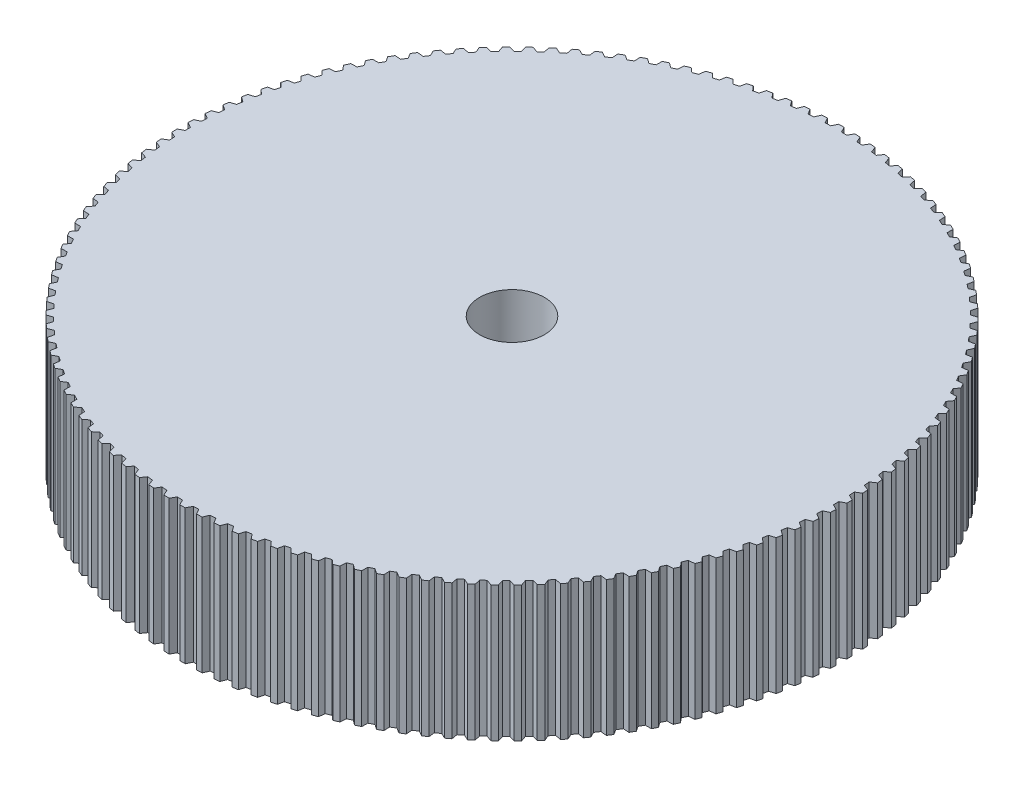
SolidWorks part; units mm, degrees
ref_plane "Front Plane" through (0, 0, 0) normal (0, 0, 1) x (1, 0, 0)
ref_plane "Top Plane" through (0, 0, 0) normal (0, 1, 0) x (1, 0, 0)
ref_plane "Right Plane" through (0, 0, 0) normal (1, 0, 0) x (0, 0, -1)
sketch "Sketch3" plane through (0, 0, 0) normal (0, 1, 0) x (1, 0, 0)
  line L0 (-0.25, 30.5) -> (0.25, 30.5)
  line L1 (0.25, 30.5) -> (0.5, 30)
  line L2 (0.5, 30) -> (-0.5, 30)
  line L3 (1.9948, 29.9378) -> (0.996, 29.9876)
  line L4 (0, 30) -> (0.5, 30)
  line L5 (1.2706, 30.4745) -> (0.996, 29.9876)
  line L6 (1.2706, 30.4745) -> (1.77, 30.4496)
  line L7 (-0.25, 30.5) -> (-0.5, 30)
  line L8 (1.77, 30.4496) -> (1.9948, 29.9378)
  line L9 (3.4846, 29.8011) -> (2.4895, 29.9007)
  line L10 (2.7881, 30.3733) -> (2.4895, 29.9007)
  line L11 (2.7881, 30.3733) -> (3.2856, 30.3235)
  line L12 (3.2856, 30.3235) -> (3.4846, 29.8011)
  line L13 (4.9657, 29.5904) -> (3.9769, 29.7394)
  line L14 (4.2986, 30.1966) -> (3.9769, 29.7394)
  line L15 (4.2986, 30.1966) -> (4.793, 30.1221)
  line L16 (4.793, 30.1221) -> (4.9657, 29.5904)
  line L17 (6.4345, 29.3061) -> (5.4543, 29.5042)
  line L18 (5.7984, 29.9448) -> (5.4543, 29.5042)
  line L19 (5.7984, 29.9448) -> (6.2885, 29.8457)
  line L20 (6.2885, 29.8457) -> (6.4345, 29.3061)
  line L21 (7.8873, 28.9489) -> (6.9182, 29.1957)
  line L22 (7.2838, 29.6185) -> (6.9182, 29.1957)
  line L23 (7.2838, 29.6185) -> (7.7684, 29.4952)
  line L24 (7.7684, 29.4952) -> (7.8873, 28.9489)
  line L25 (9.3204, 28.5198) -> (8.3649, 28.8146)
  line L26 (8.7511, 29.2187) -> (8.3649, 28.8146)
  line L27 (8.7511, 29.2187) -> (9.2289, 29.0713)
  line L28 (9.2289, 29.0713) -> (9.3204, 28.5198)
  line L29 (10.7305, 28.0198) -> (9.7908, 28.3618)
  line L30 (10.1967, 28.7461) -> (9.7908, 28.3618)
  line L31 (10.1967, 28.7461) -> (10.6665, 28.5751)
  line L32 (10.6665, 28.5751) -> (10.7305, 28.0198)
  line L33 (12.1138, 27.4501) -> (11.1923, 27.8385)
  line L34 (11.6169, 28.2021) -> (11.1923, 27.8385)
  line L35 (11.6169, 28.2021) -> (12.0776, 28.0079)
  line L36 (12.0776, 28.0079) -> (12.1138, 27.4501)
  line L37 (13.467, 26.8121) -> (12.566, 27.246)
  line L38 (13.0082, 27.588) -> (12.566, 27.246)
  line L39 (13.0082, 27.588) -> (13.4587, 27.3711)
  line L40 (13.4587, 27.3711) -> (13.467, 26.8121)
  line L41 (14.7867, 26.1075) -> (13.9085, 26.5858)
  line L42 (14.3672, 26.9053) -> (13.9085, 26.5858)
  line L43 (14.3672, 26.9053) -> (14.8063, 26.6662)
  line L44 (14.8063, 26.6662) -> (14.7867, 26.1075)
  line L45 (16.0697, 25.338) -> (15.2164, 25.8594)
  line L46 (15.6905, 26.1557) -> (15.2164, 25.8594)
  line L47 (15.6905, 26.1557) -> (16.1171, 25.895)
  line L48 (16.1171, 25.895) -> (16.0697, 25.338)
  line L49 (17.3127, 24.5055) -> (16.4865, 25.0688)
  line L50 (16.9747, 25.3411) -> (16.4865, 25.0688)
  line L51 (16.9747, 25.3411) -> (17.3878, 25.0595)
  line L52 (17.3878, 25.0595) -> (17.3127, 24.5055)
  line L53 (18.5127, 23.6121) -> (17.7156, 24.2159)
  line L54 (18.2168, 24.4635) -> (17.7156, 24.2159)
  line L55 (18.2168, 24.4635) -> (18.6153, 24.1616)
  line L56 (18.6153, 24.1616) -> (18.5127, 23.6121)
  line L57 (19.6667, 22.6599) -> (18.9006, 23.3027)
  line L58 (19.4135, 23.5251) -> (18.9006, 23.3027)
  line L59 (19.4135, 23.5251) -> (19.7965, 23.2037)
  line L60 (19.7965, 23.2037) -> (19.6667, 22.6599)
  line L61 (20.7717, 21.6515) -> (20.0387, 22.3316)
  line L62 (20.562, 22.5281) -> (20.0387, 22.3316)
  line L63 (20.562, 22.5281) -> (20.9285, 22.188)
  line L64 (20.9285, 22.188) -> (20.7717, 21.6515)
  line L65 (21.8251, 20.5892) -> (21.1269, 21.305)
  line L66 (21.6594, 21.4752) -> (21.1269, 21.305)
  line L67 (21.6594, 21.4752) -> (22.0085, 21.1173)
  line L68 (22.0085, 21.1173) -> (21.8251, 20.5892)
  line L69 (22.8243, 19.4757) -> (22.1626, 20.2255)
  line L70 (22.7029, 20.3689) -> (22.1626, 20.2255)
  line L71 (22.7029, 20.3689) -> (23.0337, 19.994)
  line L72 (23.0337, 19.994) -> (22.8243, 19.4757)
  line L73 (23.7667, 18.3138) -> (23.1432, 19.0956)
  line L74 (23.69, 19.2119) -> (23.1432, 19.0956)
  line L75 (23.69, 19.2119) -> (24.0017, 18.821)
  line L76 (24.0017, 18.821) -> (23.7667, 18.3138)
  line L77 (24.65, 17.1063) -> (24.0663, 17.9183)
  line L78 (24.6182, 18.0072) -> (24.0663, 17.9183)
  line L79 (24.6182, 18.0072) -> (24.91, 17.6012)
  line L80 (24.91, 17.6012) -> (24.65, 17.1063)
  line L81 (25.4721, 15.8564) -> (24.9295, 16.6964)
  line L82 (25.4852, 16.7577) -> (24.9295, 16.6964)
  line L83 (25.4852, 16.7577) -> (25.7564, 16.3377)
  line L84 (25.7564, 16.3377) -> (25.4721, 15.8564)
  line L85 (26.2308, 14.567) -> (25.7308, 15.433)
  line L86 (26.2888, 15.4665) -> (25.7308, 15.433)
  line L87 (26.2888, 15.4665) -> (26.5388, 15.0335)
  line L88 (26.5388, 15.0335) -> (26.2308, 14.567)
  line L89 (26.9243, 13.2414) -> (26.468, 14.1313)
  line L90 (27.027, 14.1369) -> (26.468, 14.1313)
  line L91 (27.027, 14.1369) -> (27.2551, 13.692)
  line L92 (27.2551, 13.692) -> (26.9243, 13.2414)
  line L93 (27.5508, 11.8829) -> (27.1395, 12.7944)
  line L94 (27.6981, 12.7721) -> (27.1395, 12.7944)
  line L95 (27.6981, 12.7721) -> (27.9038, 12.3164)
  line L96 (27.9038, 12.3164) -> (27.5508, 11.8829)
  line L97 (28.1089, 10.4948) -> (27.7435, 11.4257)
  line L98 (28.3003, 11.3756) -> (27.7435, 11.4257)
  line L99 (28.3003, 11.3756) -> (28.483, 10.9102)
  line L100 (28.483, 10.9102) -> (28.1089, 10.4948)
  line L101 (28.5971, 9.0806) -> (28.2786, 10.0286)
  line L102 (28.8322, 9.9508) -> (28.2786, 10.0286)
  line L103 (28.8322, 9.9508) -> (28.9914, 9.4769)
  line L104 (28.9914, 9.4769) -> (28.5971, 9.0806)
  line L105 (29.0141, 7.6439) -> (28.7433, 8.6065)
  line L106 (29.2923, 8.5013) -> (28.7433, 8.6065)
  line L107 (29.2923, 8.5013) -> (29.4277, 8.02)
  line L108 (29.4277, 8.02) -> (29.0141, 7.6439)
  line L109 (29.3591, 6.1882) -> (29.1366, 7.1631)
  line L110 (29.6797, 7.0306) -> (29.1366, 7.1631)
  line L111 (29.6797, 7.0306) -> (29.7909, 6.5432)
  line L112 (29.7909, 6.5432) -> (29.3591, 6.1882)
  line L113 (29.6311, 4.717) -> (29.4574, 5.7018)
  line L114 (29.9932, 5.5425) -> (29.4574, 5.7018)
  line L115 (29.9932, 5.5425) -> (30.08, 5.0501)
  line L116 (30.08, 5.0501) -> (29.6311, 4.717)
  line L117 (29.8293, 3.2342) -> (29.705, 4.2264)
  line L118 (30.2322, 4.0405) -> (29.705, 4.2264)
  line L119 (30.2322, 4.0405) -> (30.2944, 3.5444)
  line L120 (30.2944, 3.5444) -> (29.8293, 3.2342)
  line L121 (29.9535, 1.7433) -> (29.8787, 2.7405)
  line L122 (30.396, 2.5286) -> (29.8787, 2.7405)
  line L123 (30.396, 2.5286) -> (30.4334, 2.03)
  line L124 (30.4334, 2.03) -> (29.9535, 1.7433)
  line L125 (30.0031, 0.2481) -> (29.9782, 1.2478)
  line L126 (30.4843, 1.0103) -> (29.9782, 1.2478)
  line L127 (30.4843, 1.0103) -> (30.4968, 0.5105)
  line L128 (30.4968, 0.5105) -> (30.0031, 0.2481)
  line L129 (29.9782, -1.2478) -> (30.0031, -0.2481)
  line L130 (30.4968, -0.5105) -> (30.0031, -0.2481)
  line L131 (30.4968, -0.5105) -> (30.4843, -1.0103)
  line L132 (30.4843, -1.0103) -> (29.9782, -1.2478)
  line L133 (29.8787, -2.7405) -> (29.9535, -1.7433)
  line L134 (30.4334, -2.03) -> (29.9535, -1.7433)
  line L135 (30.4334, -2.03) -> (30.396, -2.5286)
  line L136 (30.396, -2.5286) -> (29.8787, -2.7405)
  line L137 (29.705, -4.2264) -> (29.8293, -3.2342)
  line L138 (30.2944, -3.5444) -> (29.8293, -3.2342)
  line L139 (30.2944, -3.5444) -> (30.2322, -4.0405)
  line L140 (30.2322, -4.0405) -> (29.705, -4.2264)
  line L141 (29.4574, -5.7018) -> (29.6311, -4.717)
  line L142 (30.08, -5.0501) -> (29.6311, -4.717)
  line L143 (30.08, -5.0501) -> (29.9932, -5.5425)
  line L144 (29.9932, -5.5425) -> (29.4574, -5.7018)
  line L145 (29.1366, -7.1631) -> (29.3591, -6.1882)
  line L146 (29.7909, -6.5432) -> (29.3591, -6.1882)
  line L147 (29.7909, -6.5432) -> (29.6797, -7.0306)
  line L148 (29.6797, -7.0306) -> (29.1366, -7.1631)
  line L149 (28.7433, -8.6065) -> (29.0141, -7.6439)
  line L150 (29.4277, -8.02) -> (29.0141, -7.6439)
  line L151 (29.4277, -8.02) -> (29.2923, -8.5013)
  line L152 (29.2923, -8.5013) -> (28.7433, -8.6065)
  line L153 (28.2786, -10.0286) -> (28.5971, -9.0806)
  line L154 (28.9914, -9.4769) -> (28.5971, -9.0806)
  line L155 (28.9914, -9.4769) -> (28.8322, -9.9508)
  line L156 (28.8322, -9.9508) -> (28.2786, -10.0286)
  line L157 (27.7435, -11.4257) -> (28.1089, -10.4948)
  line L158 (28.483, -10.9102) -> (28.1089, -10.4948)
  line L159 (28.483, -10.9102) -> (28.3003, -11.3756)
  line L160 (28.3003, -11.3756) -> (27.7435, -11.4257)
  line L161 (27.1395, -12.7944) -> (27.5508, -11.8829)
  line L162 (27.9038, -12.3164) -> (27.5508, -11.8829)
  line L163 (27.9038, -12.3164) -> (27.6981, -12.7721)
  line L164 (27.6981, -12.7721) -> (27.1395, -12.7944)
  line L165 (26.468, -14.1313) -> (26.9243, -13.2414)
  line L166 (27.2551, -13.692) -> (26.9243, -13.2414)
  line L167 (27.2551, -13.692) -> (27.027, -14.1369)
  line L168 (27.027, -14.1369) -> (26.468, -14.1313)
  line L169 (25.7308, -15.433) -> (26.2308, -14.567)
  line L170 (26.5388, -15.0335) -> (26.2308, -14.567)
  line L171 (26.5388, -15.0335) -> (26.2888, -15.4665)
  line L172 (26.2888, -15.4665) -> (25.7308, -15.433)
  line L173 (24.9295, -16.6964) -> (25.4721, -15.8564)
  line L174 (25.7564, -16.3377) -> (25.4721, -15.8564)
  line L175 (25.7564, -16.3377) -> (25.4852, -16.7577)
  line L176 (25.4852, -16.7577) -> (24.9295, -16.6964)
  line L177 (24.0663, -17.9183) -> (24.65, -17.1063)
  line L178 (24.91, -17.6012) -> (24.65, -17.1063)
  line L179 (24.91, -17.6012) -> (24.6182, -18.0072)
  line L180 (24.6182, -18.0072) -> (24.0663, -17.9183)
  line L181 (23.1432, -19.0956) -> (23.7667, -18.3138)
  line L182 (24.0017, -18.821) -> (23.7667, -18.3138)
  line L183 (24.0017, -18.821) -> (23.69, -19.2119)
  line L184 (23.69, -19.2119) -> (23.1432, -19.0956)
  line L185 (22.1626, -20.2255) -> (22.8243, -19.4757)
  line L186 (23.0337, -19.994) -> (22.8243, -19.4757)
  line L187 (23.0337, -19.994) -> (22.7029, -20.3689)
  line L188 (22.7029, -20.3689) -> (22.1626, -20.2255)
  line L189 (21.1269, -21.305) -> (21.8251, -20.5892)
  line L190 (22.0085, -21.1173) -> (21.8251, -20.5892)
  line L191 (22.0085, -21.1173) -> (21.6594, -21.4752)
  line L192 (21.6594, -21.4752) -> (21.1269, -21.305)
  line L193 (20.0387, -22.3316) -> (20.7717, -21.6515)
  line L194 (20.9285, -22.188) -> (20.7717, -21.6515)
  line L195 (20.9285, -22.188) -> (20.562, -22.5281)
  line L196 (20.562, -22.5281) -> (20.0387, -22.3316)
  line L197 (18.9006, -23.3027) -> (19.6667, -22.6599)
  line L198 (19.7965, -23.2037) -> (19.6667, -22.6599)
  line L199 (19.7965, -23.2037) -> (19.4135, -23.5251)
  line L200 (19.4135, -23.5251) -> (18.9006, -23.3027)
  line L201 (17.7156, -24.2159) -> (18.5127, -23.6121)
  line L202 (18.6153, -24.1616) -> (18.5127, -23.6121)
  line L203 (18.6153, -24.1616) -> (18.2168, -24.4635)
  line L204 (18.2168, -24.4635) -> (17.7156, -24.2159)
  line L205 (16.4865, -25.0688) -> (17.3127, -24.5055)
  line L206 (17.3878, -25.0595) -> (17.3127, -24.5055)
  line L207 (17.3878, -25.0595) -> (16.9747, -25.3411)
  line L208 (16.9747, -25.3411) -> (16.4865, -25.0688)
  line L209 (15.2164, -25.8594) -> (16.0697, -25.338)
  line L210 (16.1171, -25.895) -> (16.0697, -25.338)
  line L211 (16.1171, -25.895) -> (15.6905, -26.1557)
  line L212 (15.6905, -26.1557) -> (15.2164, -25.8594)
  line L213 (13.9085, -26.5858) -> (14.7867, -26.1075)
  line L214 (14.8063, -26.6662) -> (14.7867, -26.1075)
  line L215 (14.8063, -26.6662) -> (14.3672, -26.9053)
  line L216 (14.3672, -26.9053) -> (13.9085, -26.5858)
  line L217 (12.566, -27.246) -> (13.467, -26.8121)
  line L218 (13.4587, -27.3711) -> (13.467, -26.8121)
  line L219 (13.4587, -27.3711) -> (13.0082, -27.588)
  line L220 (13.0082, -27.588) -> (12.566, -27.246)
  line L221 (11.1923, -27.8385) -> (12.1138, -27.4501)
  line L222 (12.0776, -28.0079) -> (12.1138, -27.4501)
  line L223 (12.0776, -28.0079) -> (11.6169, -28.2021)
  line L224 (11.6169, -28.2021) -> (11.1923, -27.8385)
  line L225 (9.7908, -28.3618) -> (10.7305, -28.0198)
  line L226 (10.6665, -28.5751) -> (10.7305, -28.0198)
  line L227 (10.6665, -28.5751) -> (10.1967, -28.7461)
  line L228 (10.1967, -28.7461) -> (9.7908, -28.3618)
  line L229 (8.3649, -28.8146) -> (9.3204, -28.5198)
  line L230 (9.2289, -29.0713) -> (9.3204, -28.5198)
  line L231 (9.2289, -29.0713) -> (8.7511, -29.2187)
  line L232 (8.7511, -29.2187) -> (8.3649, -28.8146)
  line L233 (6.9182, -29.1957) -> (7.8873, -28.9489)
  line L234 (7.7684, -29.4952) -> (7.8873, -28.9489)
  line L235 (7.7684, -29.4952) -> (7.2838, -29.6185)
  line L236 (7.2838, -29.6185) -> (6.9182, -29.1957)
  line L237 (5.4543, -29.5042) -> (6.4345, -29.3061)
  line L238 (6.2885, -29.8457) -> (6.4345, -29.3061)
  line L239 (6.2885, -29.8457) -> (5.7984, -29.9448)
  line L240 (5.7984, -29.9448) -> (5.4543, -29.5042)
  line L241 (3.9769, -29.7394) -> (4.9657, -29.5904)
  line L242 (4.793, -30.1221) -> (4.9657, -29.5904)
  line L243 (4.793, -30.1221) -> (4.2986, -30.1966)
  line L244 (4.2986, -30.1966) -> (3.9769, -29.7394)
  line L245 (2.4895, -29.9007) -> (3.4846, -29.8011)
  line L246 (3.2856, -30.3235) -> (3.4846, -29.8011)
  line L247 (3.2856, -30.3235) -> (2.7881, -30.3733)
  line L248 (2.7881, -30.3733) -> (2.4895, -29.9007)
  line L249 (0.996, -29.9876) -> (1.9948, -29.9378)
  line L250 (1.77, -30.4496) -> (1.9948, -29.9378)
  line L251 (1.77, -30.4496) -> (1.2706, -30.4745)
  line L252 (1.2706, -30.4745) -> (0.996, -29.9876)
  line L253 (-0.5, -30) -> (0.5, -30)
  line L254 (0.25, -30.5) -> (0.5, -30)
  line L255 (0.25, -30.5) -> (-0.25, -30.5)
  line L256 (-0.25, -30.5) -> (-0.5, -30)
  line L257 (-1.9948, -29.9378) -> (-0.996, -29.9876)
  line L258 (-1.2706, -30.4745) -> (-0.996, -29.9876)
  line L259 (-1.2706, -30.4745) -> (-1.77, -30.4496)
  line L260 (-1.77, -30.4496) -> (-1.9948, -29.9378)
  line L261 (-3.4846, -29.8011) -> (-2.4895, -29.9007)
  line L262 (-2.7881, -30.3733) -> (-2.4895, -29.9007)
  line L263 (-2.7881, -30.3733) -> (-3.2856, -30.3235)
  line L264 (-3.2856, -30.3235) -> (-3.4846, -29.8011)
  line L265 (-4.9657, -29.5904) -> (-3.9769, -29.7394)
  line L266 (-4.2986, -30.1966) -> (-3.9769, -29.7394)
  line L267 (-4.2986, -30.1966) -> (-4.793, -30.1221)
  line L268 (-4.793, -30.1221) -> (-4.9657, -29.5904)
  line L269 (-6.4345, -29.3061) -> (-5.4543, -29.5042)
  line L270 (-5.7984, -29.9448) -> (-5.4543, -29.5042)
  line L271 (-5.7984, -29.9448) -> (-6.2885, -29.8457)
  line L272 (-6.2885, -29.8457) -> (-6.4345, -29.3061)
  line L273 (-7.8873, -28.9489) -> (-6.9182, -29.1957)
  line L274 (-7.2838, -29.6185) -> (-6.9182, -29.1957)
  line L275 (-7.2838, -29.6185) -> (-7.7684, -29.4952)
  line L276 (-7.7684, -29.4952) -> (-7.8873, -28.9489)
  line L277 (-9.3204, -28.5198) -> (-8.3649, -28.8146)
  line L278 (-8.7511, -29.2187) -> (-8.3649, -28.8146)
  line L279 (-8.7511, -29.2187) -> (-9.2289, -29.0713)
  line L280 (-9.2289, -29.0713) -> (-9.3204, -28.5198)
  line L281 (-10.7305, -28.0198) -> (-9.7908, -28.3618)
  line L282 (-10.1967, -28.7461) -> (-9.7908, -28.3618)
  line L283 (-10.1967, -28.7461) -> (-10.6665, -28.5751)
  line L284 (-10.6665, -28.5751) -> (-10.7305, -28.0198)
  line L285 (-12.1138, -27.4501) -> (-11.1923, -27.8385)
  line L286 (-11.6169, -28.2021) -> (-11.1923, -27.8385)
  line L287 (-11.6169, -28.2021) -> (-12.0776, -28.0079)
  line L288 (-12.0776, -28.0079) -> (-12.1138, -27.4501)
  line L289 (-13.467, -26.8121) -> (-12.566, -27.246)
  line L290 (-13.0082, -27.588) -> (-12.566, -27.246)
  line L291 (-13.0082, -27.588) -> (-13.4587, -27.3711)
  line L292 (-13.4587, -27.3711) -> (-13.467, -26.8121)
  line L293 (-14.7867, -26.1075) -> (-13.9085, -26.5858)
  line L294 (-14.3672, -26.9053) -> (-13.9085, -26.5858)
  line L295 (-14.3672, -26.9053) -> (-14.8063, -26.6662)
  line L296 (-14.8063, -26.6662) -> (-14.7867, -26.1075)
  line L297 (-16.0697, -25.338) -> (-15.2164, -25.8594)
  line L298 (-15.6905, -26.1557) -> (-15.2164, -25.8594)
  line L299 (-15.6905, -26.1557) -> (-16.1171, -25.895)
  line L300 (-16.1171, -25.895) -> (-16.0697, -25.338)
  line L301 (-17.3127, -24.5055) -> (-16.4865, -25.0688)
  line L302 (-16.9747, -25.3411) -> (-16.4865, -25.0688)
  line L303 (-16.9747, -25.3411) -> (-17.3878, -25.0595)
  line L304 (-17.3878, -25.0595) -> (-17.3127, -24.5055)
  line L305 (-18.5127, -23.6121) -> (-17.7156, -24.2159)
  line L306 (-18.2168, -24.4635) -> (-17.7156, -24.2159)
  line L307 (-18.2168, -24.4635) -> (-18.6153, -24.1616)
  line L308 (-18.6153, -24.1616) -> (-18.5127, -23.6121)
  line L309 (-19.6667, -22.6599) -> (-18.9006, -23.3027)
  line L310 (-19.4135, -23.5251) -> (-18.9006, -23.3027)
  line L311 (-19.4135, -23.5251) -> (-19.7965, -23.2037)
  line L312 (-19.7965, -23.2037) -> (-19.6667, -22.6599)
  line L313 (-20.7717, -21.6515) -> (-20.0387, -22.3316)
  line L314 (-20.562, -22.5281) -> (-20.0387, -22.3316)
  line L315 (-20.562, -22.5281) -> (-20.9285, -22.188)
  line L316 (-20.9285, -22.188) -> (-20.7717, -21.6515)
  line L317 (-21.8251, -20.5892) -> (-21.1269, -21.305)
  line L318 (-21.6594, -21.4752) -> (-21.1269, -21.305)
  line L319 (-21.6594, -21.4752) -> (-22.0085, -21.1173)
  line L320 (-22.0085, -21.1173) -> (-21.8251, -20.5892)
  line L321 (-22.8243, -19.4757) -> (-22.1626, -20.2255)
  line L322 (-22.7029, -20.3689) -> (-22.1626, -20.2255)
  line L323 (-22.7029, -20.3689) -> (-23.0337, -19.994)
  line L324 (-23.0337, -19.994) -> (-22.8243, -19.4757)
  line L325 (-23.7667, -18.3138) -> (-23.1432, -19.0956)
  line L326 (-23.69, -19.2119) -> (-23.1432, -19.0956)
  line L327 (-23.69, -19.2119) -> (-24.0017, -18.821)
  line L328 (-24.0017, -18.821) -> (-23.7667, -18.3138)
  line L329 (-24.65, -17.1063) -> (-24.0663, -17.9183)
  line L330 (-24.6182, -18.0072) -> (-24.0663, -17.9183)
  line L331 (-24.6182, -18.0072) -> (-24.91, -17.6012)
  line L332 (-24.91, -17.6012) -> (-24.65, -17.1063)
  line L333 (-25.4721, -15.8564) -> (-24.9295, -16.6964)
  line L334 (-25.4852, -16.7577) -> (-24.9295, -16.6964)
  line L335 (-25.4852, -16.7577) -> (-25.7564, -16.3377)
  line L336 (-25.7564, -16.3377) -> (-25.4721, -15.8564)
  line L337 (-26.2308, -14.567) -> (-25.7308, -15.433)
  line L338 (-26.2888, -15.4665) -> (-25.7308, -15.433)
  line L339 (-26.2888, -15.4665) -> (-26.5388, -15.0335)
  line L340 (-26.5388, -15.0335) -> (-26.2308, -14.567)
  line L341 (-26.9243, -13.2414) -> (-26.468, -14.1313)
  line L342 (-27.027, -14.1369) -> (-26.468, -14.1313)
  line L343 (-27.027, -14.1369) -> (-27.2551, -13.692)
  line L344 (-27.2551, -13.692) -> (-26.9243, -13.2414)
  line L345 (-27.5508, -11.8829) -> (-27.1395, -12.7944)
  line L346 (-27.6981, -12.7721) -> (-27.1395, -12.7944)
  line L347 (-27.6981, -12.7721) -> (-27.9038, -12.3164)
  line L348 (-27.9038, -12.3164) -> (-27.5508, -11.8829)
  line L349 (-28.1089, -10.4948) -> (-27.7435, -11.4257)
  line L350 (-28.3003, -11.3756) -> (-27.7435, -11.4257)
  line L351 (-28.3003, -11.3756) -> (-28.483, -10.9102)
  line L352 (-28.483, -10.9102) -> (-28.1089, -10.4948)
  line L353 (-28.5971, -9.0806) -> (-28.2786, -10.0286)
  line L354 (-28.8322, -9.9508) -> (-28.2786, -10.0286)
  line L355 (-28.8322, -9.9508) -> (-28.9914, -9.4769)
  line L356 (-28.9914, -9.4769) -> (-28.5971, -9.0806)
  line L357 (-29.0141, -7.6439) -> (-28.7433, -8.6065)
  line L358 (-29.2923, -8.5013) -> (-28.7433, -8.6065)
  line L359 (-29.2923, -8.5013) -> (-29.4277, -8.02)
  line L360 (-29.4277, -8.02) -> (-29.0141, -7.6439)
  line L361 (-29.3591, -6.1882) -> (-29.1366, -7.1631)
  line L362 (-29.6797, -7.0306) -> (-29.1366, -7.1631)
  line L363 (-29.6797, -7.0306) -> (-29.7909, -6.5432)
  line L364 (-29.7909, -6.5432) -> (-29.3591, -6.1882)
  line L365 (-29.6311, -4.717) -> (-29.4574, -5.7018)
  line L366 (-29.9932, -5.5425) -> (-29.4574, -5.7018)
  line L367 (-29.9932, -5.5425) -> (-30.08, -5.0501)
  line L368 (-30.08, -5.0501) -> (-29.6311, -4.717)
  line L369 (-29.8293, -3.2342) -> (-29.705, -4.2264)
  line L370 (-30.2322, -4.0405) -> (-29.705, -4.2264)
  line L371 (-30.2322, -4.0405) -> (-30.2944, -3.5444)
  line L372 (-30.2944, -3.5444) -> (-29.8293, -3.2342)
  line L373 (-29.9535, -1.7433) -> (-29.8787, -2.7405)
  line L374 (-30.396, -2.5286) -> (-29.8787, -2.7405)
  line L375 (-30.396, -2.5286) -> (-30.4334, -2.03)
  line L376 (-30.4334, -2.03) -> (-29.9535, -1.7433)
  line L377 (-30.0031, -0.2481) -> (-29.9782, -1.2478)
  line L378 (-30.4843, -1.0103) -> (-29.9782, -1.2478)
  line L379 (-30.4843, -1.0103) -> (-30.4968, -0.5105)
  line L380 (-30.4968, -0.5105) -> (-30.0031, -0.2481)
  line L381 (-29.9782, 1.2478) -> (-30.0031, 0.2481)
  line L382 (-30.4968, 0.5105) -> (-30.0031, 0.2481)
  line L383 (-30.4968, 0.5105) -> (-30.4843, 1.0103)
  line L384 (-30.4843, 1.0103) -> (-29.9782, 1.2478)
  line L385 (-29.8787, 2.7405) -> (-29.9535, 1.7433)
  line L386 (-30.4334, 2.03) -> (-29.9535, 1.7433)
  line L387 (-30.4334, 2.03) -> (-30.396, 2.5286)
  line L388 (-30.396, 2.5286) -> (-29.8787, 2.7405)
  line L389 (-29.705, 4.2264) -> (-29.8293, 3.2342)
  line L390 (-30.2944, 3.5444) -> (-29.8293, 3.2342)
  line L391 (-30.2944, 3.5444) -> (-30.2322, 4.0405)
  line L392 (-30.2322, 4.0405) -> (-29.705, 4.2264)
  line L393 (-29.4574, 5.7018) -> (-29.6311, 4.717)
  line L394 (-30.08, 5.0501) -> (-29.6311, 4.717)
  line L395 (-30.08, 5.0501) -> (-29.9932, 5.5425)
  line L396 (-29.9932, 5.5425) -> (-29.4574, 5.7018)
  line L397 (-29.1366, 7.1631) -> (-29.3591, 6.1882)
  line L398 (-29.7909, 6.5432) -> (-29.3591, 6.1882)
  line L399 (-29.7909, 6.5432) -> (-29.6797, 7.0306)
  line L400 (-29.6797, 7.0306) -> (-29.1366, 7.1631)
  line L401 (-28.7433, 8.6065) -> (-29.0141, 7.6439)
  line L402 (-29.4277, 8.02) -> (-29.0141, 7.6439)
  line L403 (-29.4277, 8.02) -> (-29.2923, 8.5013)
  line L404 (-29.2923, 8.5013) -> (-28.7433, 8.6065)
  line L405 (-28.2786, 10.0286) -> (-28.5971, 9.0806)
  line L406 (-28.9914, 9.4769) -> (-28.5971, 9.0806)
  line L407 (-28.9914, 9.4769) -> (-28.8322, 9.9508)
  line L408 (-28.8322, 9.9508) -> (-28.2786, 10.0286)
  line L409 (-27.7435, 11.4257) -> (-28.1089, 10.4948)
  line L410 (-28.483, 10.9102) -> (-28.1089, 10.4948)
  line L411 (-28.483, 10.9102) -> (-28.3003, 11.3756)
  line L412 (-28.3003, 11.3756) -> (-27.7435, 11.4257)
  line L413 (-27.1395, 12.7944) -> (-27.5508, 11.8829)
  line L414 (-27.9038, 12.3164) -> (-27.5508, 11.8829)
  line L415 (-27.9038, 12.3164) -> (-27.6981, 12.7721)
  line L416 (-27.6981, 12.7721) -> (-27.1395, 12.7944)
  line L417 (-26.468, 14.1313) -> (-26.9243, 13.2414)
  line L418 (-27.2551, 13.692) -> (-26.9243, 13.2414)
  line L419 (-27.2551, 13.692) -> (-27.027, 14.1369)
  line L420 (-27.027, 14.1369) -> (-26.468, 14.1313)
  line L421 (-25.7308, 15.433) -> (-26.2308, 14.567)
  line L422 (-26.5388, 15.0335) -> (-26.2308, 14.567)
  line L423 (-26.5388, 15.0335) -> (-26.2888, 15.4665)
  line L424 (-26.2888, 15.4665) -> (-25.7308, 15.433)
  line L425 (-24.9295, 16.6964) -> (-25.4721, 15.8564)
  line L426 (-25.7564, 16.3377) -> (-25.4721, 15.8564)
  line L427 (-25.7564, 16.3377) -> (-25.4852, 16.7577)
  line L428 (-25.4852, 16.7577) -> (-24.9295, 16.6964)
  line L429 (-24.0663, 17.9183) -> (-24.65, 17.1063)
  line L430 (-24.91, 17.6012) -> (-24.65, 17.1063)
  line L431 (-24.91, 17.6012) -> (-24.6182, 18.0072)
  line L432 (-24.6182, 18.0072) -> (-24.0663, 17.9183)
  line L433 (-23.1432, 19.0956) -> (-23.7667, 18.3138)
  line L434 (-24.0017, 18.821) -> (-23.7667, 18.3138)
  line L435 (-24.0017, 18.821) -> (-23.69, 19.2119)
  line L436 (-23.69, 19.2119) -> (-23.1432, 19.0956)
  line L437 (-22.1626, 20.2255) -> (-22.8243, 19.4757)
  line L438 (-23.0337, 19.994) -> (-22.8243, 19.4757)
  line L439 (-23.0337, 19.994) -> (-22.7029, 20.3689)
  line L440 (-22.7029, 20.3689) -> (-22.1626, 20.2255)
  line L441 (-21.1269, 21.305) -> (-21.8251, 20.5892)
  line L442 (-22.0085, 21.1173) -> (-21.8251, 20.5892)
  line L443 (-22.0085, 21.1173) -> (-21.6594, 21.4752)
  line L444 (-21.6594, 21.4752) -> (-21.1269, 21.305)
  line L445 (-20.0387, 22.3316) -> (-20.7717, 21.6515)
  line L446 (-20.9285, 22.188) -> (-20.7717, 21.6515)
  line L447 (-20.9285, 22.188) -> (-20.562, 22.5281)
  line L448 (-20.562, 22.5281) -> (-20.0387, 22.3316)
  line L449 (-18.9006, 23.3027) -> (-19.6667, 22.6599)
  line L450 (-19.7965, 23.2037) -> (-19.6667, 22.6599)
  line L451 (-19.7965, 23.2037) -> (-19.4135, 23.5251)
  line L452 (-19.4135, 23.5251) -> (-18.9006, 23.3027)
  line L453 (-17.7156, 24.2159) -> (-18.5127, 23.6121)
  line L454 (-18.6153, 24.1616) -> (-18.5127, 23.6121)
  line L455 (-18.6153, 24.1616) -> (-18.2168, 24.4635)
  line L456 (-18.2168, 24.4635) -> (-17.7156, 24.2159)
  line L457 (-16.4865, 25.0688) -> (-17.3127, 24.5055)
  line L458 (-17.3878, 25.0595) -> (-17.3127, 24.5055)
  line L459 (-17.3878, 25.0595) -> (-16.9747, 25.3411)
  line L460 (-16.9747, 25.3411) -> (-16.4865, 25.0688)
  line L461 (-15.2164, 25.8594) -> (-16.0697, 25.338)
  line L462 (-16.1171, 25.895) -> (-16.0697, 25.338)
  line L463 (-16.1171, 25.895) -> (-15.6905, 26.1557)
  line L464 (-15.6905, 26.1557) -> (-15.2164, 25.8594)
  line L465 (-13.9085, 26.5858) -> (-14.7867, 26.1075)
  line L466 (-14.8063, 26.6662) -> (-14.7867, 26.1075)
  line L467 (-14.8063, 26.6662) -> (-14.3672, 26.9053)
  line L468 (-14.3672, 26.9053) -> (-13.9085, 26.5858)
  line L469 (-12.566, 27.246) -> (-13.467, 26.8121)
  line L470 (-13.4587, 27.3711) -> (-13.467, 26.8121)
  line L471 (-13.4587, 27.3711) -> (-13.0082, 27.588)
  line L472 (-13.0082, 27.588) -> (-12.566, 27.246)
  line L473 (-11.1923, 27.8385) -> (-12.1138, 27.4501)
  line L474 (-12.0776, 28.0079) -> (-12.1138, 27.4501)
  line L475 (-12.0776, 28.0079) -> (-11.6169, 28.2021)
  line L476 (-11.6169, 28.2021) -> (-11.1923, 27.8385)
  line L477 (-9.7908, 28.3618) -> (-10.7305, 28.0198)
  line L478 (-10.6665, 28.5751) -> (-10.7305, 28.0198)
  line L479 (-10.6665, 28.5751) -> (-10.1967, 28.7461)
  line L480 (-10.1967, 28.7461) -> (-9.7908, 28.3618)
  line L481 (-8.3649, 28.8146) -> (-9.3204, 28.5198)
  line L482 (-9.2289, 29.0713) -> (-9.3204, 28.5198)
  line L483 (-9.2289, 29.0713) -> (-8.7511, 29.2187)
  line L484 (-8.7511, 29.2187) -> (-8.3649, 28.8146)
  line L485 (-6.9182, 29.1957) -> (-7.8873, 28.9489)
  line L486 (-7.7684, 29.4952) -> (-7.8873, 28.9489)
  line L487 (-7.7684, 29.4952) -> (-7.2838, 29.6185)
  line L488 (-7.2838, 29.6185) -> (-6.9182, 29.1957)
  line L489 (-5.4543, 29.5042) -> (-6.4345, 29.3061)
  line L490 (-6.2885, 29.8457) -> (-6.4345, 29.3061)
  line L491 (-6.2885, 29.8457) -> (-5.7984, 29.9448)
  line L492 (-5.7984, 29.9448) -> (-5.4543, 29.5042)
  line L493 (-3.9769, 29.7394) -> (-4.9657, 29.5904)
  line L494 (-4.793, 30.1221) -> (-4.9657, 29.5904)
  line L495 (-4.793, 30.1221) -> (-4.2986, 30.1966)
  line L496 (-4.2986, 30.1966) -> (-3.9769, 29.7394)
  line L497 (-2.4895, 29.9007) -> (-3.4846, 29.8011)
  line L498 (-3.2856, 30.3235) -> (-3.4846, 29.8011)
  line L499 (-3.2856, 30.3235) -> (-2.7881, 30.3733)
  line L500 (-2.7881, 30.3733) -> (-2.4895, 29.9007)
  line L501 (-0.996, 29.9876) -> (-1.9948, 29.9378)
  line L502 (-1.77, 30.4496) -> (-1.9948, 29.9378)
  line L503 (-1.77, 30.4496) -> (-1.2706, 30.4745)
  line L504 (-1.2706, 30.4745) -> (-0.996, 29.9876)
  line L505 (-0.996, 29.9876) -> (-0.5, 30)
  line L506 (0.5, 30) -> (0.996, 29.9876)
  line L507 (1.9948, 29.9378) -> (2.4895, 29.9007)
  line L508 (3.4846, 29.8011) -> (3.9769, 29.7394)
  line L509 (4.9657, 29.5904) -> (5.4543, 29.5042)
  line L510 (6.4345, 29.3061) -> (6.9182, 29.1957)
  line L511 (7.8873, 28.9489) -> (8.3649, 28.8146)
  line L512 (9.3204, 28.5198) -> (9.7908, 28.3618)
  line L513 (10.7305, 28.0198) -> (11.1923, 27.8385)
  line L514 (12.1138, 27.4501) -> (12.566, 27.246)
  line L515 (13.467, 26.8121) -> (13.9085, 26.5858)
  line L516 (14.7867, 26.1075) -> (15.2164, 25.8594)
  line L517 (16.0697, 25.338) -> (16.4865, 25.0688)
  line L518 (17.3127, 24.5055) -> (17.7156, 24.2159)
  line L519 (18.5127, 23.6121) -> (18.9006, 23.3027)
  line L520 (19.6667, 22.6599) -> (20.0387, 22.3316)
  line L521 (20.7717, 21.6515) -> (21.1269, 21.305)
  line L522 (21.8251, 20.5892) -> (22.1626, 20.2255)
  line L523 (22.8243, 19.4757) -> (23.1432, 19.0956)
  line L524 (23.7667, 18.3138) -> (24.0663, 17.9183)
  line L525 (24.65, 17.1063) -> (24.9295, 16.6964)
  line L526 (25.4721, 15.8564) -> (25.7308, 15.433)
  line L527 (26.2308, 14.567) -> (26.468, 14.1313)
  line L528 (26.9243, 13.2414) -> (27.1395, 12.7944)
  line L529 (27.5508, 11.8829) -> (27.7435, 11.4257)
  line L530 (28.1089, 10.4948) -> (28.2786, 10.0286)
  line L531 (28.5971, 9.0806) -> (28.7433, 8.6065)
  line L532 (29.0141, 7.6439) -> (29.1366, 7.1631)
  line L533 (29.3591, 6.1882) -> (29.4574, 5.7018)
  line L534 (29.6311, 4.717) -> (29.705, 4.2264)
  line L535 (29.8293, 3.2342) -> (29.8787, 2.7405)
  line L536 (29.9535, 1.7433) -> (29.9782, 1.2478)
  line L537 (30.0031, 0.2481) -> (30.0031, -0.2481)
  line L538 (29.9782, -1.2478) -> (29.9535, -1.7433)
  line L539 (29.8787, -2.7405) -> (29.8293, -3.2342)
  line L540 (29.705, -4.2264) -> (29.6311, -4.717)
  line L541 (29.4574, -5.7018) -> (29.3591, -6.1882)
  line L542 (29.1366, -7.1631) -> (29.0141, -7.6439)
  line L543 (28.7433, -8.6065) -> (28.5971, -9.0806)
  line L544 (28.2786, -10.0286) -> (28.1089, -10.4948)
  line L545 (27.7435, -11.4257) -> (27.5508, -11.8829)
  line L546 (27.1395, -12.7944) -> (26.9243, -13.2414)
  line L547 (26.468, -14.1313) -> (26.2308, -14.567)
  line L548 (25.7308, -15.433) -> (25.4721, -15.8564)
  line L549 (24.9295, -16.6964) -> (24.65, -17.1063)
  line L550 (24.0663, -17.9183) -> (23.7667, -18.3138)
  line L551 (23.1432, -19.0956) -> (22.8243, -19.4757)
  line L552 (22.1626, -20.2255) -> (21.8251, -20.5892)
  line L553 (21.1269, -21.305) -> (20.7717, -21.6515)
  line L554 (20.0387, -22.3316) -> (19.6667, -22.6599)
  line L555 (18.9006, -23.3027) -> (18.5127, -23.6121)
  line L556 (17.7156, -24.2159) -> (17.3127, -24.5055)
  line L557 (16.4865, -25.0688) -> (16.0697, -25.338)
  line L558 (15.2164, -25.8594) -> (14.7867, -26.1075)
  line L559 (13.9085, -26.5858) -> (13.467, -26.8121)
  line L560 (12.566, -27.246) -> (12.1138, -27.4501)
  line L561 (11.1923, -27.8385) -> (10.7305, -28.0198)
  line L562 (9.7908, -28.3618) -> (9.3204, -28.5198)
  line L563 (8.3649, -28.8146) -> (7.8873, -28.9489)
  line L564 (6.9182, -29.1957) -> (6.4345, -29.3061)
  line L565 (5.4543, -29.5042) -> (4.9657, -29.5904)
  line L566 (3.9769, -29.7394) -> (3.4846, -29.8011)
  line L567 (2.4895, -29.9007) -> (1.9948, -29.9378)
  line L568 (0.996, -29.9876) -> (0.5, -30)
  line L569 (-0.5, -30) -> (-0.996, -29.9876)
  line L570 (-1.9948, -29.9378) -> (-2.4895, -29.9007)
  line L571 (-3.4846, -29.8011) -> (-3.9769, -29.7394)
  line L572 (-4.9657, -29.5904) -> (-5.4543, -29.5042)
  line L573 (-6.4345, -29.3061) -> (-6.9182, -29.1957)
  line L574 (-7.8873, -28.9489) -> (-8.3649, -28.8146)
  line L575 (-9.3204, -28.5198) -> (-9.7908, -28.3618)
  line L576 (-10.7305, -28.0198) -> (-11.1923, -27.8385)
  line L577 (-12.1138, -27.4501) -> (-12.566, -27.246)
  line L578 (-13.467, -26.8121) -> (-13.9085, -26.5858)
  line L579 (-14.7867, -26.1075) -> (-15.2164, -25.8594)
  line L580 (-16.0697, -25.338) -> (-16.4865, -25.0688)
  line L581 (-17.3127, -24.5055) -> (-17.7156, -24.2159)
  line L582 (-18.5127, -23.6121) -> (-18.9006, -23.3027)
  line L583 (-19.6667, -22.6599) -> (-20.0387, -22.3316)
  line L584 (-20.7717, -21.6515) -> (-21.1269, -21.305)
  line L585 (-21.8251, -20.5892) -> (-22.1626, -20.2255)
  line L586 (-22.8243, -19.4757) -> (-23.1432, -19.0956)
  line L587 (-23.7667, -18.3138) -> (-24.0663, -17.9183)
  line L588 (-24.65, -17.1063) -> (-24.9295, -16.6964)
  line L589 (-25.4721, -15.8564) -> (-25.7308, -15.433)
  line L590 (-26.2308, -14.567) -> (-26.468, -14.1313)
  line L591 (-26.9243, -13.2414) -> (-27.1395, -12.7944)
  line L592 (-27.5508, -11.8829) -> (-27.7435, -11.4257)
  line L593 (-28.1089, -10.4948) -> (-28.2786, -10.0286)
  line L594 (-28.5971, -9.0806) -> (-28.7433, -8.6065)
  line L595 (-29.0141, -7.6439) -> (-29.1366, -7.1631)
  line L596 (-29.3591, -6.1882) -> (-29.4574, -5.7018)
  line L597 (-29.6311, -4.717) -> (-29.705, -4.2264)
  line L598 (-29.8293, -3.2342) -> (-29.8787, -2.7405)
  line L599 (-29.9535, -1.7433) -> (-29.9782, -1.2478)
  line L600 (-30.0031, -0.2481) -> (-30.0031, 0.2481)
  line L601 (-29.9782, 1.2478) -> (-29.9535, 1.7433)
  line L602 (-29.8787, 2.7405) -> (-29.8293, 3.2342)
  line L603 (-29.705, 4.2264) -> (-29.6311, 4.717)
  line L604 (-29.4574, 5.7018) -> (-29.3591, 6.1882)
  line L605 (-29.1366, 7.1631) -> (-29.0141, 7.6439)
  line L606 (-28.7433, 8.6065) -> (-28.5971, 9.0806)
  line L607 (-28.2786, 10.0286) -> (-28.1089, 10.4948)
  line L608 (-27.7435, 11.4257) -> (-27.5508, 11.8829)
  line L609 (-27.1395, 12.7944) -> (-26.9243, 13.2414)
  line L610 (-26.468, 14.1313) -> (-26.2308, 14.567)
  line L611 (-25.7308, 15.433) -> (-25.4721, 15.8564)
  line L612 (-24.9295, 16.6964) -> (-24.65, 17.1063)
  line L613 (-24.0663, 17.9183) -> (-23.7667, 18.3138)
  line L614 (-23.1432, 19.0956) -> (-22.8243, 19.4757)
  line L615 (-22.1626, 20.2255) -> (-21.8251, 20.5892)
  line L616 (-21.1269, 21.305) -> (-20.7717, 21.6515)
  line L617 (-20.0387, 22.3316) -> (-19.6667, 22.6599)
  line L618 (-18.9006, 23.3027) -> (-18.5127, 23.6121)
  line L619 (-17.7156, 24.2159) -> (-17.3127, 24.5055)
  line L620 (-16.4865, 25.0688) -> (-16.0697, 25.338)
  line L621 (-15.2164, 25.8594) -> (-14.7867, 26.1075)
  line L622 (-13.9085, 26.5858) -> (-13.467, 26.8121)
  line L623 (-12.566, 27.246) -> (-12.1138, 27.4501)
  line L624 (-11.1923, 27.8385) -> (-10.7305, 28.0198)
  line L625 (-9.7908, 28.3618) -> (-9.3204, 28.5198)
  line L626 (-8.3649, 28.8146) -> (-7.8873, 28.9489)
  line L627 (-6.9182, 29.1957) -> (-6.4345, 29.3061)
  line L628 (-5.4543, 29.5042) -> (-4.9657, 29.5904)
  line L629 (-3.9769, 29.7394) -> (-3.4846, 29.8011)
  line L630 (-2.4895, 29.9007) -> (-1.9948, 29.9378)
  point P507 (0, 0)
  point P758 (0, 0)
  dimension "D1" = 126
  dimension "D2" = 126
extrude "Boss-Extrude3" add sketch "Sketch3" along normal blind 12.5 contours L630 L497 L629 L493 L628 L489 L627 L485 L626 L481 L625 L477 L624 L473 L623 L469 L622 L465 L621 L461 L620 L457 L619 L453 L618 L449 L617 L445 L616 L441 L615 L437 L614 L433 L613 L429 L612 L425 L611 L421 L610 L417 L609 L413 L608 L409 L607 L405 L606 L401 L605 | L284 L283 L282 L281 | L288 L287 L286 L285 | L292 L291 L290 L289 | L296 L295 L294 L293 | L300 L299 L298 L297 | L304 L303 L302 L301 | L272 L271 L270 L269 | L252 L251 L250 L249 | L248 L247 L246 L245 | L232 L231 L230 L229 | L224 L223 L222 L221 | L220 L219 L218 L217 | L208 L207 L206 L205 | L200 L199 L198 L197 | L192 L191 L190 L189 | L188 L187 L186 L185 | L184 L183 L182 L181 | L180 L179 L178 L177 | L176 L175 L174 L173 | L172 L171 L170 L169 | L156 L155 L154 L153 | L152 L151 L150 L149 | L140 L139 L138 L137 | L136 L135 L134 L133 | L132 L131 L130 L129 | L128 L127 L126 L125 | L124 L123 L122 L121 | L108 L107 L106 L105 | L104 L103 L102 L101 | L100 L99 L98 L97 | L96 L95 L94 L93 | L92 L91 L90 L89 | L84 L83 L82 L81 | L80 L79 L78 L77 | L76 L75 L74 L73 | L68 L67 L66 L65 | L64 L63 L62 L61 | L52 L51 L50 L49 | L48 L47 L46 L45 | L44 L43 L42 L41 | L40 L39 L38 L37 | L36 L35 L34 L33 | L28 L27 L26 L25 | L24 L23 L22 L21 | L20 L19 L18 L17 | L16 L15 L14 L13 | L12 L11 L10 L9 | L8 L6 L5 L3 | L0 L7 L2 L1 | L504 L503 L502 L501 | L500 L499 L498 L497 | L496 L495 L494 L493 | L492 L491 L490 L489 | L488 L487 L486 L485 | L484 L483 L482 L481 | L480 L479 L478 L477 | L476 L475 L474 L473 | L472 L471 L470 L469 | L468 L467 L466 L465 | L464 L463 L462 L461 | L460 L459 L458 L457 | L456 L455 L454 L453 | L452 L451 L450 L449 | L448 L447 L446 L445 | L444 L443 L442 L441 | L436 L435 L434 L433 | L432 L431 L430 L429 | L428 L427 L426 L425 | L424 L423 L422 L421 | L420 L419 L418 L417 | L416 L415 L414 L413 | L408 L407 L406 L405 | L400 L399 L398 L397 | L396 L395 L394 L393 | L392 L391 L390 L389 | L388 L387 L386 L385 | L384 L383 L382 L381 | L380 L379 L378 L377 | L376 L375 L374 L373 | L372 L371 L370 L369 | L364 L363 L362 L361 | L360 L359 L358 L357 | L356 L355 L354 L353 | L352 L351 L350 L349 | L348 L347 L346 L345 | L344 L343 L342 L341 | L340 L339 L338 L337 | L332 L331 L330 L329 | L306 L305 L308 L307 | L310 L309 L312 L311 | L316 L313 L314 L315 | L320 L317 L318 L319 | L324 L321 L322 L323 | L328 L325 L326 L327 | L279 L280 L277 L278 | L273 L274 L275 L276 | L268 L265 L266 L267 | L261 L262 L263 L264 | L260 L257 L258 L259 | L253 L254 L255 L256 | L241 L242 L243 L244 | L237 L238 L239 L240 | L235 L236 L233 L234 | L227 L228 L225 L226 | L215 L216 L213 L214 | L209 L210 L211 L212 | L202 L201 L204 L203 | L196 L193 L194 L195 | L167 L168 L165 L166 | L163 L164 L161 L162 | L159 L160 L157 L158 | L145 L146 L147 L148 | L141 L142 L143 L144 | L117 L118 L119 L120 | L113 L114 L115 L116 | L109 L110 L111 L112 | L87 L88 L85 L86 | L70 L69 L72 L71 | L58 L57 L60 L59 | L54 L53 L56 L55 | L31 L32 L29 L30 | L365 L366 L367 L368 | L334 L333 L336 L335
sketch "Sketch4" plane through (0, 0, 0) normal (0, 1, 0) x (1, 0, 0)
  circle A0 centre (0, 0) radius 3
extrude "Cut-Extrude2" cut sketch "Sketch4" along normal blind 12.5
